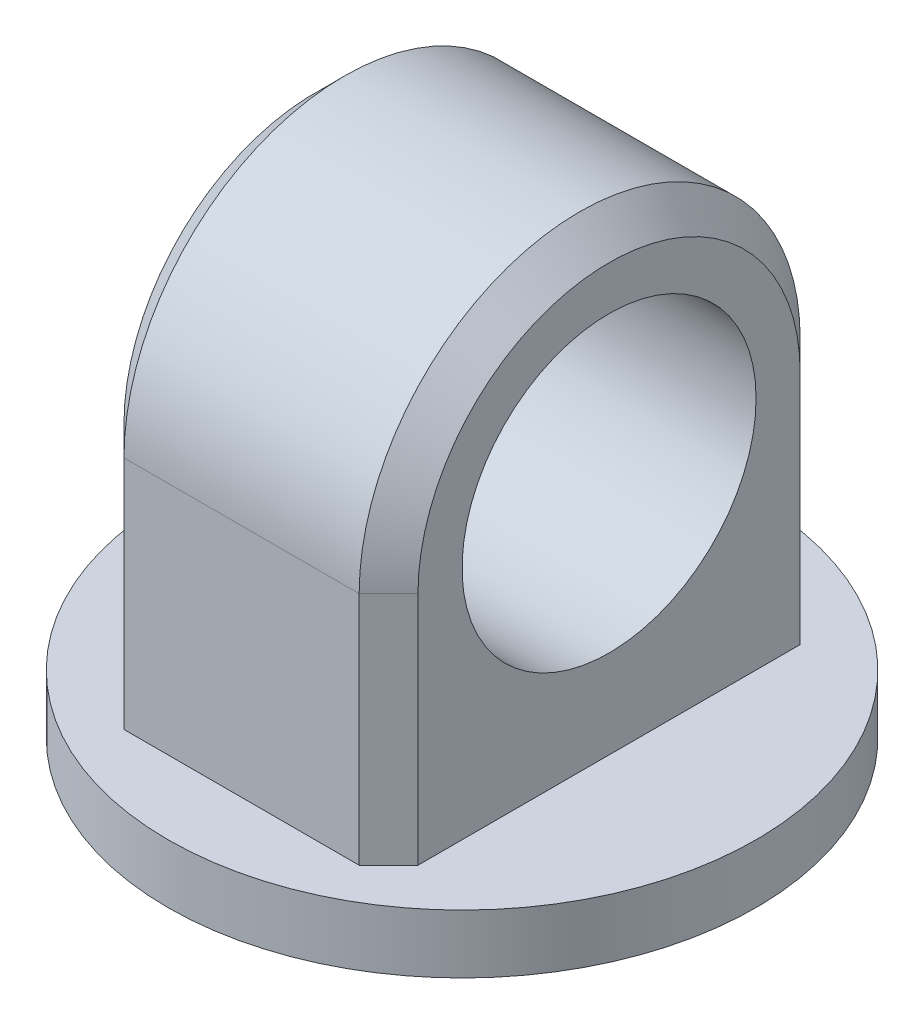
SolidWorks part; units mm, degrees
ref_plane "Front Plane" through (0, 0, 0) normal (0, 0, 1) x (1, 0, 0)
ref_plane "Top Plane" through (0, 0, 0) normal (0, 1, 0) x (1, 0, 0)
ref_plane "Right Plane" through (0, 0, 0) normal (1, 0, 0) x (0, 0, -1)
sketch "Sketch1" plane through (0, 0, 0) normal (0, 1, 0) x (1, 0, 0)
  circle A0 centre (0, 0) radius 50
  dimension "D1" = 100
extrude "Boss-Extrude1" add sketch "Sketch1" along normal blind 10
sketch "Sketch2" plane through (0, 10, 0) normal (0, 1, 0) x (1, 0, 0)
  line L1 (-25, 37.5) -> (25, 37.5)
  line L2 (-25, 37.5) -> (-25, -37.5)
  line L3 (-25, -37.5) -> (25, -37.5)
  line L4 (25, 37.5) -> (25, -37.5)
  line L5 (-25, 37.5) -> (25, -37.5) construction
  line L6 (-25, -37.5) -> (25, 37.5) construction
  point P0 (0, 0)
  dimension "D1" = 75
  dimension "D2" = 50
extrude "Boss-Extrude2" add sketch "Sketch2" along normal blind 80
sketch "Sketch3" plane through (25, 0, 0) normal (1, 0, 0) x (0, 0, -1)
  line L0 (0, 90) -> (0, 10) construction
  line L1 (-37.5, 90) -> (37.5, 90) construction
  line L2 (50, 10) -> (-50, 10) construction
  circle A0 centre (0, 50) radius 25
  dimension "D2" = 50
  dimension "D1" = 40
extrude "Cut-Extrude4" cut sketch "Sketch3" against normal through all
sketch "Sketch4" plane through (25, 0, 0) normal (1, 0, 0) x (0, 0, -1)
  line L2 (-37.5, 50) -> (-37.5, 90)
  line L3 (-37.5, 90) -> (37.5, 90)
  line L4 (37.5, 90) -> (37.5, 50)
  arc A2 (37.5, 50) -> (-37.5, 50) centre (0, 50) ccw
extrude "Cut-Extrude5" cut sketch "Sketch4" against normal through all
chamfer "Chamfer1" distance 5 angle 45 6 edges at (-25, 30, 37.5) (-25, 30, -37.5) (-25, 87.5, 0) (25, 30, 37.5) (25, 30, -37.5) (25, 87.5, 0)
